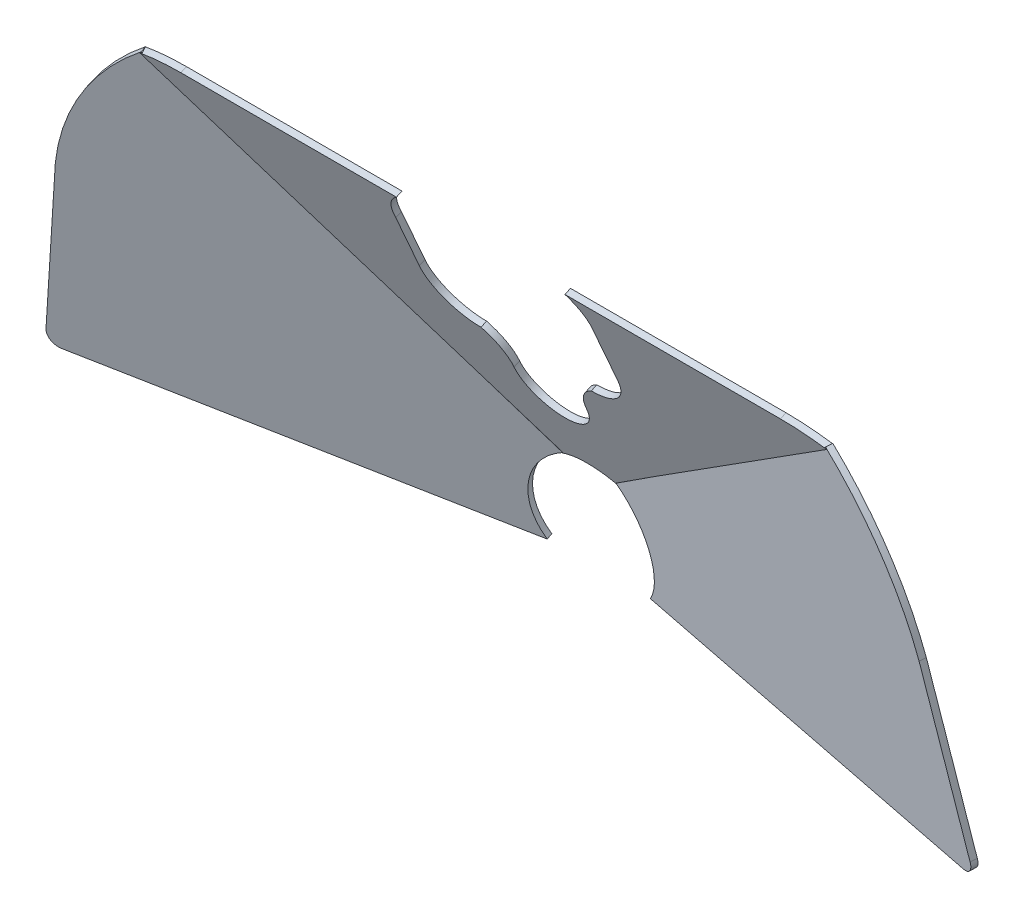
SolidWorks part; units mm, degrees
material "1060 Alloy"
ref_plane "Front Plane" through (0, 0, 0) normal (0, 0, 1) x (1, 0, 0)
ref_plane "Top Plane" through (0, 0, 0) normal (0, 1, 0) x (1, 0, 0)
ref_plane "Right Plane" through (0, 0, 0) normal (1, 0, 0) x (0, 0, -1)
ref_plane "Support Plane" through (0, -411.4156, 932.7779) normal (0, -0.4036, 0.915) x (1, 0, 0)
ref_plane "Dash Plane" through (0, -403.2154, 914.186) normal (0, -0.4036, 0.915) x (1, 0, 0)
sketch "Sketch1" plane through (0, -403.2154, 914.186) normal (0, -0.4036, 0.915) x (1, 0, 0)
  line L0 (0, -72.1957) -> (0, 72.1957) construction
  line L2 (41.0905, 1205.3028) -> (41.0905, 1181.1728)
  line L27 (142.4152, 1217.2039) -> (11.6024, 1107.5425)
  line L34 (-41.0905, 1205.3028) -> (-41.0905, 1181.1728)
  line L37 (0, -28.3995) -> (0, 28.3995) construction
  line L38 (-142.4152, 1217.2039) -> (-11.6024, 1107.5425)
  line L39 (-124.2827, 1219.9528) -> (-34.9221, 1219.9528)
  line L40 (124.2827, 1219.9528) -> (34.9221, 1219.9528)
  arc A7 (-15.0239, 1148.3975) -> (15.0239, 1148.3975) centre (0, 1148.3975) ccw
  arc A10 (-15.0239, 1148.3975) -> (-22.86, 1162.9423) centre (-32.4403, 1148.3975) ccw
  arc A15 (15.0239, 1148.3975) -> (22.86, 1162.9423) centre (32.4403, 1148.3975) cw
  arc A16 (11.6024, 1107.5425) -> (-11.6024, 1107.5425) centre (0, 1086.5812) ccw
  arc A17 (-124.2827, 1219.9528) -> (-142.4152, 1217.2039) centre (-124.2827, 1158.7758) ccw
  arc A18 (-34.9221, 1219.9528) -> (-41.0905, 1205.3028) centre (-24.2774, 1206.8473) ccw
  arc A19 (124.2827, 1219.9528) -> (142.4152, 1217.2039) centre (124.2827, 1158.7758) cw
  arc A20 (34.9221, 1219.9528) -> (41.0905, 1205.3028) centre (24.2774, 1206.8473) cw
  ellipse E2 centre (-93.9509, 1156.061) end of major axis (-176.5009, 1156.061) minor radius 75.5296 (-93.9509, 1231.5906) -> (-175.5975, 1167.2048) ccw construction
  spline S2 degree 2 poles (41.0905, 1181.1728) (41.0905, 1179.5004) (40.7861, 1177.8555) (40.6273, 1176.9969) (40.3867, 1176.1565) (40.1404, 1175.2957) (39.8105, 1174.4622) (39.4741, 1173.6124) (39.0538, 1172.7996) (38.6274, 1171.9749) (38.1188, 1171.1969) (37.6054, 1170.4115) (37.0133, 1169.6821) (36.4187, 1168.9497) (35.7509, 1168.2819) (35.0838, 1167.6148) (34.3506, 1167.0195) (33.6222, 1166.428) (32.8359, 1165.9139) (32.0588, 1165.4059) (31.2332, 1164.9789) (30.4213, 1164.5591) (29.5705, 1164.2223) (28.7381, 1163.8927) (27.8763, 1163.646) (27.0368, 1163.4057) (26.1773, 1163.2466) (24.5328, 1162.9423) (22.86, 1162.9423) knots 0 0 0 0.125 0.125 0.1875 0.1875 0.25 0.25 0.3125 0.3125 0.375 0.375 0.4375 0.4375 0.5 0.5 0.5625 0.5625 0.625 0.625 0.6875 0.6875 0.75 0.75 0.8125 0.8125 0.875 0.875 1 1 1
  spline S5 degree 2 poles (-41.0905, 1181.1728) (-41.0905, 1179.5004) (-40.7861, 1177.8555) (-40.6273, 1176.9969) (-40.3867, 1176.1565) (-40.1404, 1175.2957) (-39.8105, 1174.4622) (-39.4741, 1173.6124) (-39.0538, 1172.7996) (-38.6274, 1171.9749) (-38.1188, 1171.1969) (-37.6054, 1170.4115) (-37.0133, 1169.6821) (-36.4187, 1168.9497) (-35.7509, 1168.2819) (-35.0838, 1167.6148) (-34.3506, 1167.0195) (-33.6222, 1166.428) (-32.8359, 1165.9139) (-32.0588, 1165.4059) (-31.2332, 1164.9789) (-30.4213, 1164.5591) (-29.5705, 1164.2223) (-28.7381, 1163.8927) (-27.8763, 1163.646) (-27.0368, 1163.4057) (-26.1773, 1163.2466) (-24.5328, 1162.9423) (-22.86, 1162.9423) knots 0 0 0 0.125 0.125 0.1875 0.1875 0.25 0.25 0.3125 0.3125 0.375 0.375 0.4375 0.4375 0.5 0.5 0.5625 0.5625 0.625 0.625 0.6875 0.6875 0.75 0.75 0.8125 0.8125 0.875 0.875 1 1 1
  point P48 (0, 1223.5332)
ref_plane "Square Tube Face" through (-250.8736, -190.1271, 1181.5856) normal (0.2052, 0.1555, -0.9663) x (-0.9787, 0.0329, -0.2025)
ref_plane "Plane9" through (250.4567, -189.8112, 1179.6221) normal (-0.2052, 0.1555, -0.9663) x (-0.9787, -0.0326, 0.2026)
extrude "Boss-Extrude1" add sketch "Sketch1" along normal blind 2.54
sketch "Sketch2" plane through (250.4567, -189.8112, 1179.6221) normal (-0.2052, 0.1555, -0.9663) x (-0.9787, -0.0326, 0.2026)
  line L1 (438.8244, 866.074) -> (451.6069, 795.4219)
  line L2 (501.2087, 521.2612) -> (438.8244, 866.074) construction
  line L4 (400.876, 924.729) -> (267.1553, 818.6336)
  line L5 (446.6999, 789.3568) -> (277.7529, 780.2416)
  arc A1 (451.6069, 795.4219) -> (446.6999, 789.3568) centre (446.5385, 794.5049) cw
  arc A2 (267.1553, 818.6336) -> (277.7529, 780.2416) centre (256.3033, 794.9794) cw
  arc A3 (400.876, 924.729) -> (438.8244, 866.074) centre (342.4332, 845.3146) cw
extrude "Boss-Extrude2" add sketch "Sketch2" along normal blind 2.54 separate body
mirror "Mirror7" about plane through (0, 0, 0) normal (1, 0, 0) of "Boss-Extrude1", "Boss-Extrude2"
